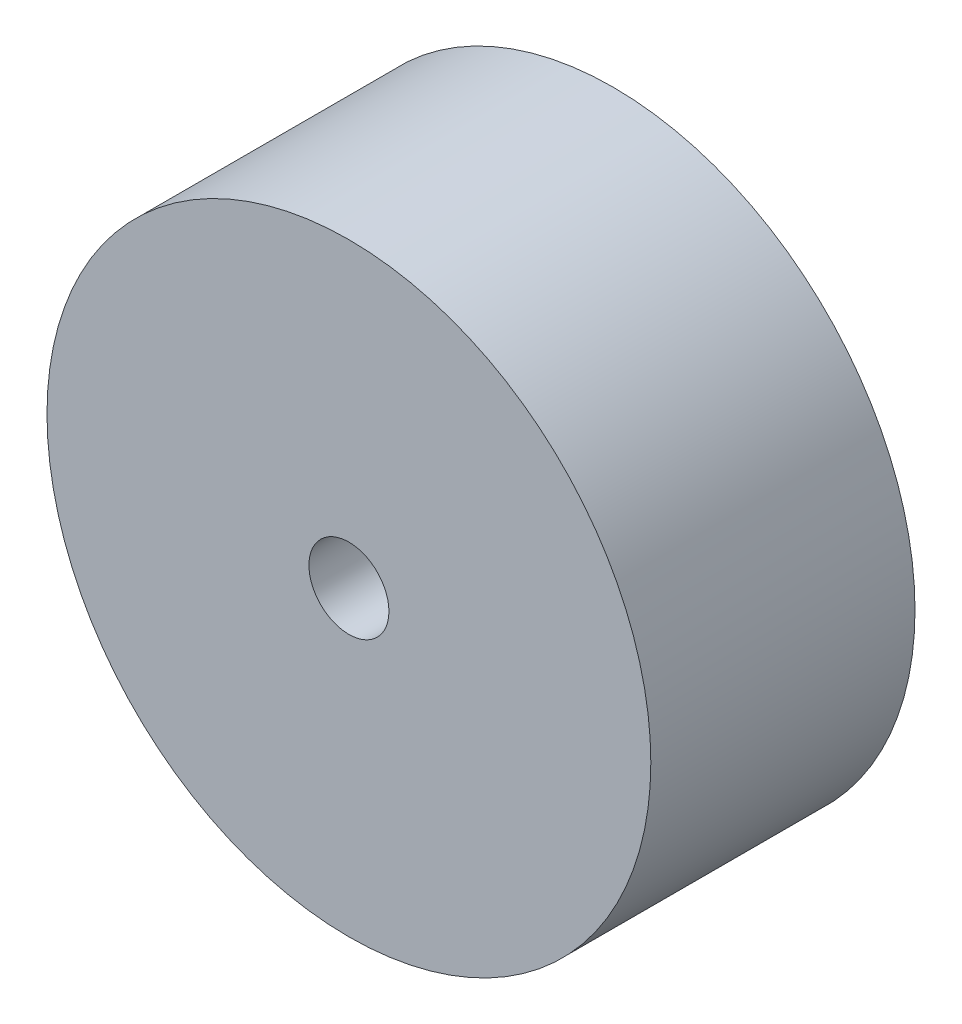
SolidWorks part; units mm, degrees
ref_plane "Front Plane" through (0, 0, 0) normal (0, 0, 1) x (1, 0, 0)
ref_plane "Top Plane" through (0, 0, 0) normal (0, 1, 0) x (1, 0, 0)
ref_plane "Right Plane" through (0, 0, 0) normal (1, 0, 0) x (0, 0, -1)
sketch "Sketch1" plane through (0, 0, 0) normal (0, 0, 1) x (1, 0, 0)
  circle A0 centre (0, 0) radius 25.4
  dimension "D1" = 50.8
extrude "Boss-Extrude1" add sketch "Sketch1" along normal blind 22.225
sketch "Sketch2" plane through (0, 0, 22.225) normal (0, 0, 1) x (1, 0, 0)
  circle A0 centre (0, 0) radius 3.3655
  dimension "D1" = 6.731
extrude "Cut-Extrude1" cut sketch "Sketch2" against normal through all
